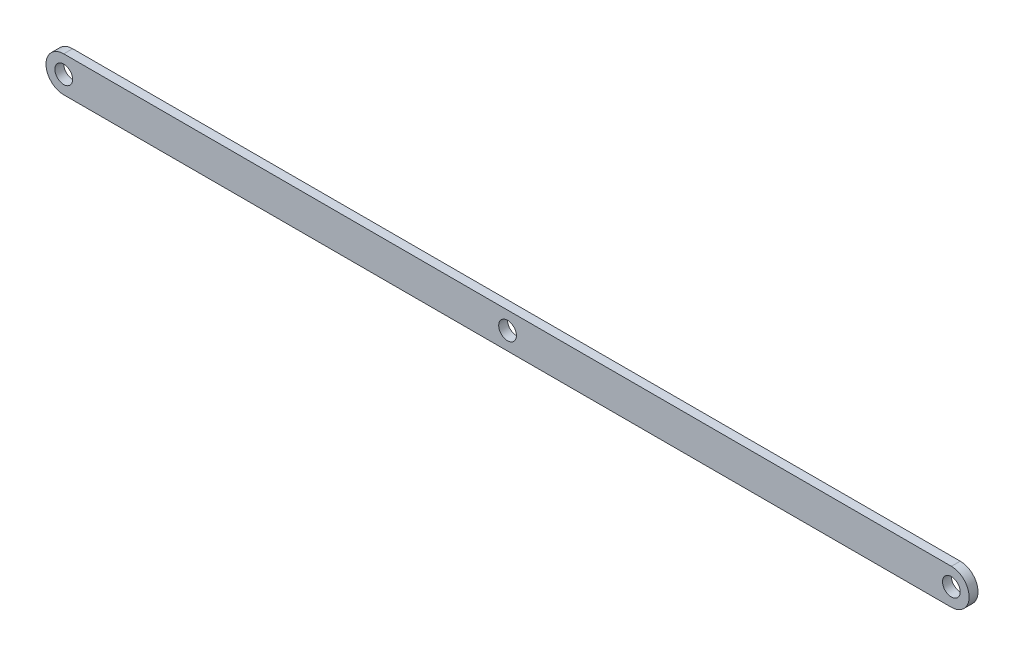
SolidWorks part; units mm, degrees
ref_plane "Front Plane" through (0, 0, 0) normal (0, 0, 1) x (1, 0, 0)
ref_plane "Top Plane" through (0, 0, 0) normal (0, 1, 0) x (1, 0, 0)
ref_plane "Right Plane" through (0, 0, 0) normal (1, 0, 0) x (0, 0, -1)
sketch "Sketch1" plane through (0, 0, 0) normal (0, 0, 1) x (1, 0, 0)
  line L0 (-250, 0) -> (250, 0) construction
  line L1 (-250, 10) -> (250, 10)
  line L2 (-250, -10) -> (250, -10)
  arc A0 (-250, 10) -> (-250, -10) centre (-250, 0) ccw
  arc A1 (250, -10) -> (250, 10) centre (250, 0) ccw
  circle A2 centre (-250, 0) radius 5
  circle A3 centre (250, 0) radius 5
  circle A4 centre (0, 0) radius 5
  point P2 (0, 0)
  dimension "D3" = 10
  dimension "D4" = 10
  dimension "D5" = 10
  dimension "D1" = 500
  dimension "D2" = 20
extrude "Boss-Extrude1" add sketch "Sketch1" along normal blind 5
